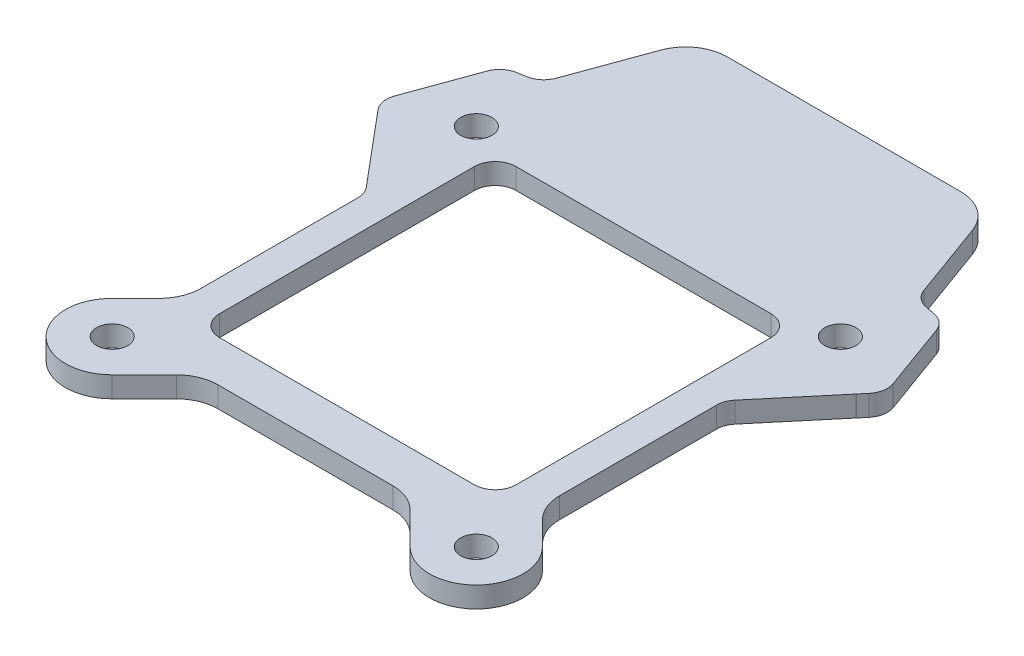
SolidWorks part; units mm, degrees
ref_plane "Front Plane" through (0, 0, 0) normal (0, 0, 1) x (1, 0, 0)
ref_plane "Top Plane" through (0, 0, 0) normal (0, 1, 0) x (1, 0, 0)
ref_plane "Right Plane" through (0, 0, 0) normal (1, 0, 0) x (0, 0, -1)
sketch "Sketch1" plane through (0, 0, 0) normal (0, 1, 0) x (1, 0, 0)
  line L0 (-14.8584, -17.6109) -> (-14.8584, 6.8891)
  line L1 (11.6416, -19.6109) -> (-12.8584, -19.6109)
  line L2 (13.6416, 6.8891) -> (13.6416, -17.6109)
  line L3 (-12.8584, 8.8891) -> (11.6416, 8.8891)
  line L4 (16.6416, -1.3288) -> (16.6416, -16.4126)
  line L5 (17.8132, -19.241) -> (20.0736, -21.5014)
  line L6 (13.7096, -27.8654) -> (10.6268, -24.7825)
  line L7 (7.7983, -23.6109) -> (-9.0151, -23.6109)
  line L8 (-11.8435, -24.7825) -> (-14.9264, -27.8654)
  line L9 (-21.2904, -21.5014) -> (-19.0299, -19.241)
  line L10 (-17.8584, -16.4126) -> (-17.8584, -1.3288)
  line L11 (-18.3263, -0.0432) -> (-23.6443, 6.2946)
  line L12 (-23.6567, 6.3095) -> (-24.2134, 6.9729)
  line L13 (-24.5607, 8.9425) -> (-22.1911, 15.4529)
  line L14 (-20.659, 16.7385) -> (-19.8062, 16.8889)
  line L15 (-18.2741, 18.1744) -> (-15.5941, 25.5375)
  line L16 (-11.8354, 28.1694) -> (10.6186, 28.1694)
  line L17 (14.3774, 25.5375) -> (17.0573, 18.1744)
  line L18 (18.5894, 16.8889) -> (19.4423, 16.7385)
  line L19 (20.9744, 15.4529) -> (23.344, 8.9425)
  line L20 (22.9967, 6.9729) -> (22.44, 6.3095)
  line L21 (22.4276, 6.2946) -> (17.1095, -0.0432)
  arc A0 (-14.8584, -17.6109) -> (-12.8584, -19.6109) centre (-12.8584, -17.6109) ccw
  arc A1 (11.6416, -19.6109) -> (13.6416, -17.6109) centre (11.6416, -17.6109) ccw
  arc A2 (-12.8584, 8.8891) -> (-14.8584, 6.8891) centre (-12.8584, 6.8891) ccw
  arc A3 (16.6416, -16.4126) -> (17.8132, -19.241) centre (20.6416, -16.4126) ccw
  arc A4 (13.7096, -27.8654) -> (20.0736, -21.5014) centre (16.8916, -24.6834) ccw
  arc A5 (10.6268, -24.7825) -> (7.7983, -23.6109) centre (7.7983, -27.6109) ccw
  arc A6 (-9.0151, -23.6109) -> (-11.8435, -24.7825) centre (-9.0151, -27.6109) ccw
  arc A7 (-21.2904, -21.5014) -> (-14.9264, -27.8654) centre (-18.1084, -24.6834) ccw
  arc A8 (-19.0299, -19.241) -> (-17.8584, -16.4126) centre (-21.8584, -16.4126) ccw
  arc A9 (-17.8584, -1.3288) -> (-18.3263, -0.0432) centre (-19.8584, -1.3288) ccw
  arc A10 (-23.6443, 6.2946) -> (-23.6567, 6.3095) centre (-25.1887, 5.0237) ccw
  arc A11 (-24.5607, 8.9425) -> (-24.2134, 6.9729) centre (-22.6813, 8.2585) ccw
  arc A12 (-20.659, 16.7385) -> (-22.1911, 15.4529) centre (-20.3117, 14.7689) ccw
  arc A13 (-19.8062, 16.8889) -> (-18.2741, 18.1744) centre (-20.1535, 18.8585) ccw
  arc A14 (-11.8354, 28.1694) -> (-15.5941, 25.5375) centre (-11.8354, 24.1694) ccw
  arc A15 (14.3774, 25.5375) -> (10.6186, 28.1694) centre (10.6186, 24.1694) ccw
  arc A16 (17.0573, 18.1744) -> (18.5894, 16.8889) centre (18.9367, 18.8585) ccw
  arc A17 (20.9744, 15.4529) -> (19.4423, 16.7385) centre (19.095, 14.7689) ccw
  arc A18 (22.9967, 6.9729) -> (23.344, 8.9425) centre (21.4646, 8.2585) ccw
  arc A19 (22.44, 6.3095) -> (22.4276, 6.2946) centre (23.9719, 5.0237) ccw
  arc A20 (17.1095, -0.0432) -> (16.6416, -1.3288) centre (18.6416, -1.3288) ccw
  circle A21 centre (-18.1084, 10.3166) radius 3.5 construction
  circle A22 centre (16.8916, 10.3166) radius 3.5 construction
  circle A23 centre (16.8916, -24.6834) radius 3.5 construction
  circle A24 centre (-18.1084, -24.6834) radius 3.5 construction
  arc A25 (13.6416, 6.8891) -> (11.6416, 8.8891) centre (11.6416, 6.8891) ccw
  circle A26 centre (-18.1084, 10.3166) radius 1.5
  circle A27 centre (-18.1084, -24.6834) radius 1.5
  circle A28 centre (16.8916, -24.6834) radius 1.5
  circle A29 centre (16.8916, 10.3166) radius 1.5
extrude "Boss-Extrude1" add sketch "Sketch1" along normal blind 2
